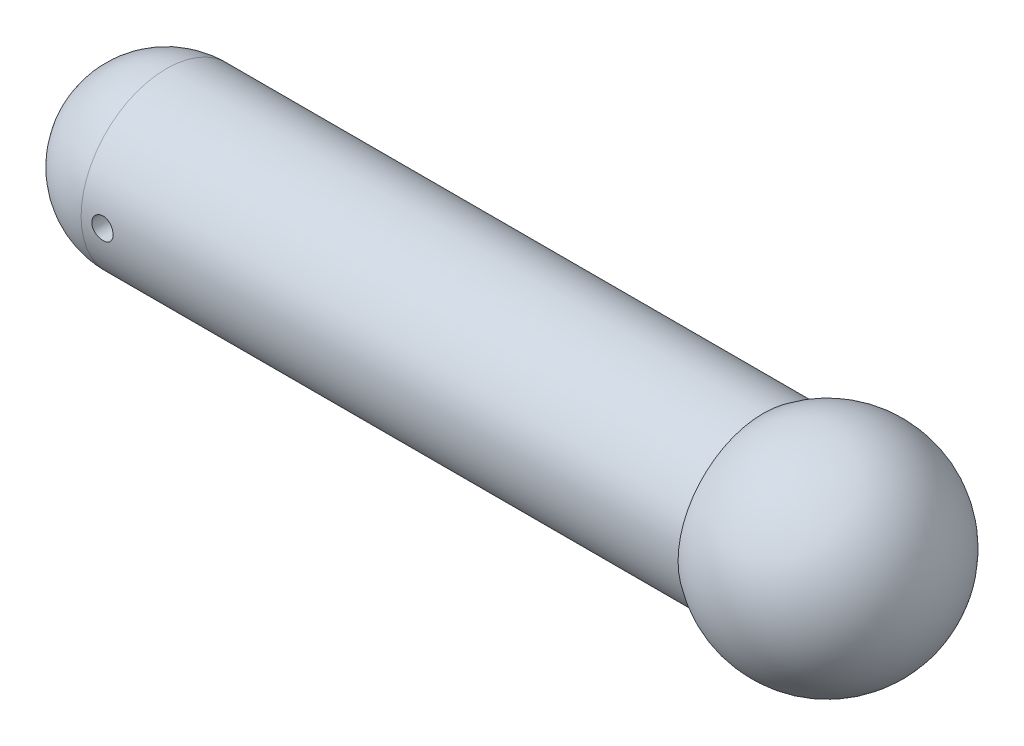
SolidWorks part; units mm, degrees
material "Aleación 2014"
ref_plane "Alzado" through (0, 0, 0) normal (0, 0, 1) x (1, 0, 0)
ref_plane "Planta" through (0, 0, 0) normal (0, 1, 0) x (1, 0, 0)
ref_plane "Vista lateral" through (0, 0, 0) normal (1, 0, 0) x (0, 0, -1)
sketch "Croquis3" plane through (0, 0, 0) normal (0, 1, 0) x (1, 0, 0)
  line L0 (-63.0853, 0) -> (72.028, 0) construction
  line L2 (-52.9193, 0) -> (-32.9193, 0) construction
  line L5 (147.0807, 0) -> (47.0807, 0) construction
  line L6 (-32.9193, 20) -> (107.0807, 20)
  line L8 (147.0807, 0) -> (122.0807, 0) construction
  line L11 (-52.9193, 0) -> (147.0807, 0)
  arc A4 (-32.9193, 20) -> (-52.9193, 0) centre (-32.9193, 0) ccw
  arc A7 (147.0807, 0) -> (107.0807, 20) centre (122.0807, 0) ccw
  dimension "D2" = 25
  dimension "D4" = 200
revolve "Revolución10" add sketch "Croquis3" angle 360 about L0
sketch "Croquis6" plane through (0, 0, 0) normal (0, 0, 1) x (1, 0, 0)
  line L2 (-32.9193, 0) -> (-27.9193, 0) construction
  circle A3 centre (-27.9193, 0) radius 2.5
  dimension "D2" = 5
  dimension "D1" = 5
extrude "Cortar-Extruir1" cut sketch "Croquis6" against normal through all both and the other way through all
